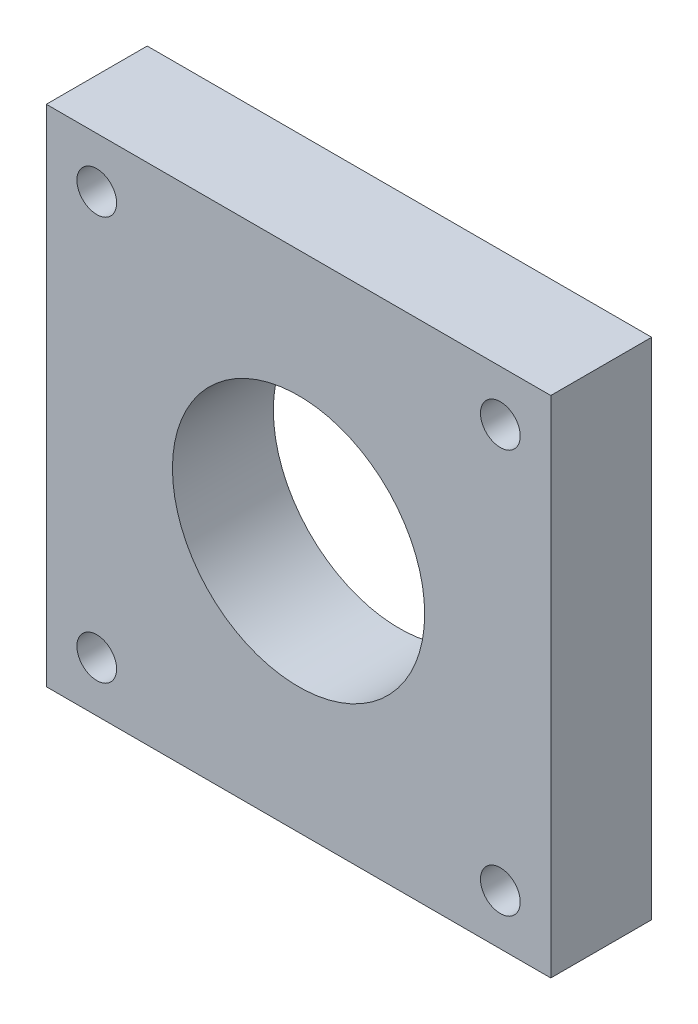
SolidWorks part; units mm, degrees
ref_plane "Front Plane" through (0, 0, 0) normal (0, 0, 1) x (1, 0, 0)
ref_plane "Top Plane" through (0, 0, 0) normal (0, 1, 0) x (1, 0, 0)
ref_plane "Right Plane" through (0, 0, 0) normal (1, 0, 0) x (0, 0, -1)
sketch "Sketch1" plane through (0, 0, 0) normal (0, 0, 1) x (1, 0, 0)
  line L1 (-25.4, 25.4) -> (25.4, 25.4)
  line L2 (-25.4, 25.4) -> (-25.4, -25.4)
  line L3 (-25.4, -25.4) -> (25.4, -25.4)
  line L4 (25.4, 25.4) -> (25.4, -25.4)
  line L5 (-25.4, 25.4) -> (25.4, -25.4) construction
  line L6 (-25.4, -25.4) -> (25.4, 25.4) construction
  circle A0 centre (-20.32, 20.32) radius 2
  circle A1 centre (20.32, 20.32) radius 2
  circle A2 centre (20.32, -20.32) radius 2
  circle A3 centre (-20.32, -20.32) radius 2
  circle A4 centre (0, 0) radius 12.7
  point P0 (0, 0)
  dimension "D3" = 4
  dimension "D5" = 25.4
  dimension "D1" = 50.8
  dimension "D2" = 50.8
  dimension "D4" = 5.08
extrude "Boss-Extrude1" add sketch "Sketch1" along normal blind 10.16
